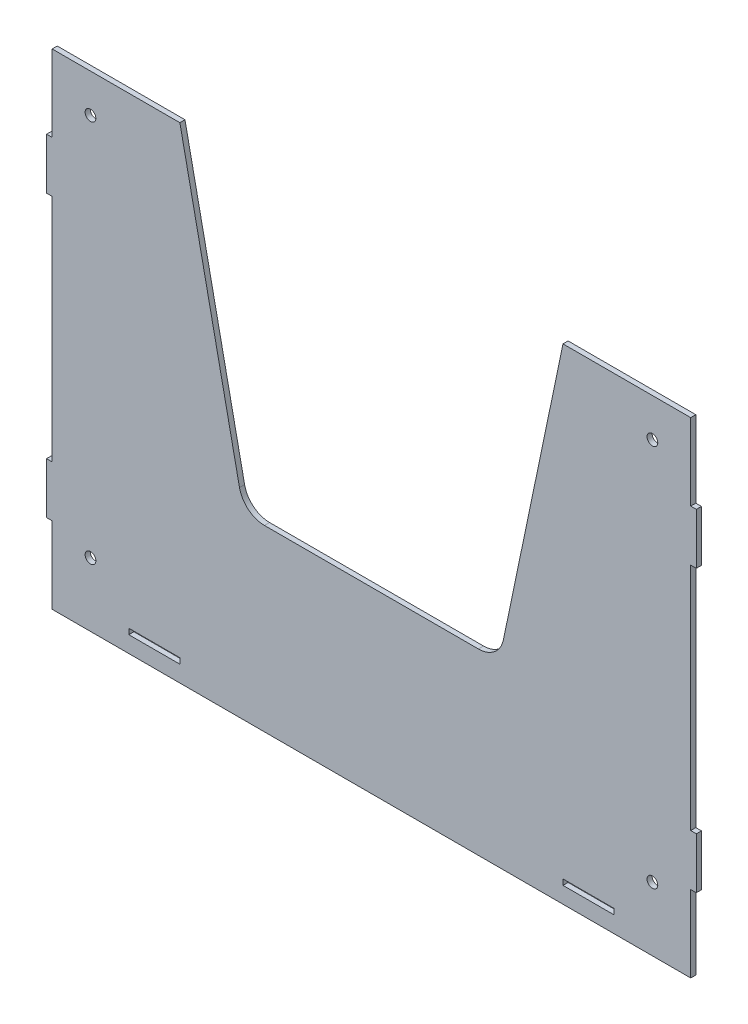
SolidWorks part; units mm, degrees
ref_plane "Front Plane" through (0, 0, 0) normal (0, 0, 1) x (1, 0, 0)
ref_plane "Top Plane" through (0, 0, 0) normal (0, 1, 0) x (1, 0, 0)
ref_plane "Right Plane" through (0, 0, 0) normal (1, 0, 0) x (0, 0, -1)
sketch "Sketch1" plane through (0, 0, 0) normal (0, 0, 1) x (1, 0, 0)
  line L0 (-125, -10.4333) -> (-125, 19.5667) construction
  line L1 (125, -10.4333) -> (-125, -10.4333)
  line L2 (125, -10.4333) -> (125, 19.5667)
  line L3 (125, -10.4333) -> (125, 19.5667) construction
  line L4 (-125, -10.4333) -> (-125, 19.5667)
  line L5 (125, 179.5667) -> (75, 179.5667)
  line L6 (75, 179.5667) -> (50, 59.5667)
  line L7 (50, 59.5667) -> (-50, 59.5667)
  line L8 (-50, 59.5667) -> (-75, 179.5667)
  line L9 (-75, 179.5667) -> (-125, 179.5667)
  line L10 (75, -2.9333) -> (95, -2.9333) construction
  line L11 (85, -1.8333) -> (85, -4.0333) construction
  line L12 (-85, -1.8333) -> (-85, -4.0333) construction
  line L13 (95, -4.0333) -> (75, -4.0333)
  line L14 (95, -4.0333) -> (95, -1.8333)
  line L15 (95, -1.8333) -> (75, -1.8333)
  line L16 (75, -4.0333) -> (75, -1.8333)
  line L17 (-95, -2.9333) -> (-75, -2.9333) construction
  line L20 (-75, -4.0333) -> (-95, -4.0333)
  line L21 (-75, -4.0333) -> (-75, -1.8333)
  line L22 (-75, -1.8333) -> (-95, -1.8333)
  line L23 (-95, -4.0333) -> (-95, -1.8333)
  line L27 (-125, 19.5667) -> (-127.2, 19.5667)
  line L29 (-125, 39.5667) -> (-127.2, 39.5667)
  line L30 (-127.2, 19.5667) -> (-127.2, 39.5667)
  line L31 (-125, 149.5667) -> (-125, 179.5667)
  line L32 (-125, 129.5667) -> (-127.2, 129.5667)
  line L33 (-125, 39.5667) -> (-125, 129.5667)
  line L34 (-125, 149.5667) -> (-127.2, 149.5667)
  line L35 (-127.2, 129.5667) -> (-127.2, 149.5667)
  line L36 (125, 39.5667) -> (127.2, 39.5667)
  line L38 (125, 19.5667) -> (127.2, 19.5667)
  line L39 (127.2, 39.5667) -> (127.2, 19.5667)
  line L40 (125, 149.5667) -> (125, 179.5667)
  line L41 (125, 149.5667) -> (127.2, 149.5667)
  line L42 (125, 39.5667) -> (125, 129.5667)
  line L43 (125, 129.5667) -> (127.2, 129.5667)
  line L44 (127.2, 149.5667) -> (127.2, 129.5667)
  point P16 (-75, -2.9333)
  point P19 (-85, -1.8333)
  point P20 (-85, -4.0333)
  point P23 (-95, -2.9333)
  point P38 (95, -2.9333)
  point P39 (75, -2.9333)
  point P48 (85, -1.8333)
  point P49 (85, -4.0333)
  point P58 (85, -2.9333)
  point P61 (-85, -2.9333)
  dimension "D1" = 50
  dimension "D2" = 50
  dimension "D3" = 100
  dimension "D4" = 50
  dimension "D5" = 190
  dimension "D6" = 70
  dimension "D7" = 7.5
  dimension "D8" = 20
  dimension "D11" = 20
  dimension "D12" = 20
  dimension "D13" = 30
  dimension "D14" = 30
  dimension "D15" = 20
  dimension "D16" = 20
  dimension "D17" = 30
  dimension "D18" = 30
  dimension "D19" = 2.2
  dimension "D20" = 7.5
  dimension "D21" = 40
  dimension "D22" = 40
extrude "Boss-Extrude1" add sketch "Sketch1" along normal blind 2
fillet "Fillet1" radius 10 2 edges at (50, 59.5667, 1) (-50, 59.5667, 1)
sketch "Sketch2" plane through (0, 0, 2) normal (0, 0, 1) x (1, 0, 0)
  line L0 (-125, -10.4333) -> (125, -10.4333) construction
  line L1 (-125, 19.5667) -> (-125, -10.4333) construction
  line L2 (125, -10.4333) -> (125, 19.5667) construction
  line L4 (-75, 179.5667) -> (-125, 179.5667) construction
  line L5 (125, 179.5667) -> (75, 179.5667) construction
  circle A0 centre (-110, 14.5667) radius 2.1
  circle A1 centre (110, 14.5667) radius 2.1
  circle A2 centre (110, 164.5667) radius 2.1
  circle A3 centre (-110, 164.5667) radius 2.1
  dimension "D1" = 4.2
  dimension "D2" = 4.2
  dimension "D3" = 25
  dimension "D5" = 25
  dimension "D6" = 15
  dimension "D7" = 4.2
  dimension "D8" = 4.2
  dimension "D9" = 15
  dimension "D4" = 15
  dimension "D10" = 15
extrude "Cut-Extrude1" cut sketch "Sketch2" against normal blind 5
